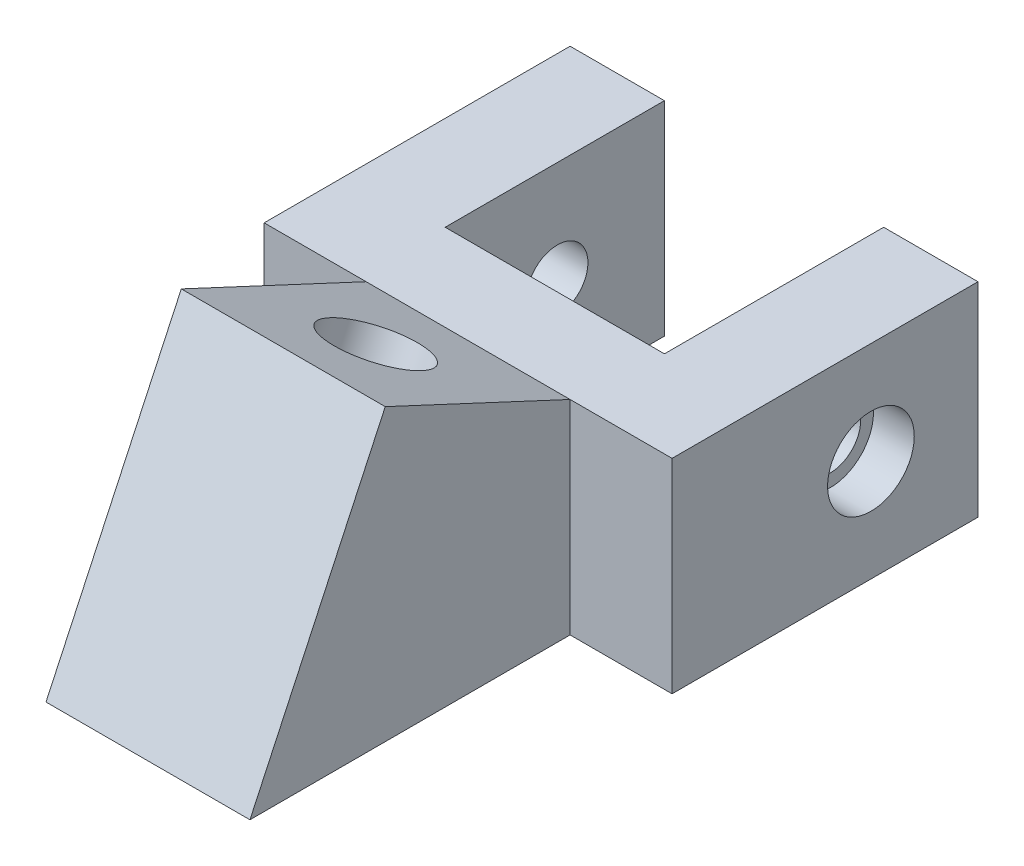
SolidWorks part; units mm, degrees
ref_plane "Front Plane" through (0, 0, 0) normal (0, 0, 1) x (1, 0, 0)
ref_plane "Top Plane" through (0, 0, 0) normal (0, 1, 0) x (1, 0, 0)
ref_plane "Right Plane" through (0, 0, 0) normal (1, 0, 0) x (0, 0, -1)
sketch "Sketch1" plane through (0, 0, 0) normal (0, 1, 0) x (1, 0, 0)
  line L0 (-10.75, 15) -> (-10.75, -6.5)
  line L1 (-20, -15) -> (20, -15)
  line L2 (-20, -15) -> (-20, 15)
  line L3 (-20, 15) -> (-10.75, 15)
  line L4 (20, -15) -> (20, 15)
  line L5 (-20, -15) -> (20, 15) construction
  line L6 (-20, 15) -> (20, -15) construction
  line L7 (-10.75, -6.5) -> (10.75, -6.5)
  line L8 (10.75, -6.5) -> (10.75, 15)
  line L9 (10.75, 15) -> (20, 15)
  point P0 (0, 0)
  dimension "D1" = 40
  dimension "D2" = 30
  dimension "D3" = 21.5
  dimension "D4" = 21.5
  dimension "D5" = 10.75
extrude "Boss-Extrude1" add sketch "Sketch1" along normal blind 20 contours L7 L8 L9 L4 L1 L2 L3 L0
sketch "Sketch2" plane through (0, 0, 0) normal (1, 0, 0) x (0, 0, -1)
  line L0 (-15, 20) -> (-15, 0) construction
  line L1 (-15, 20) -> (-15, 0)
  line L2 (-15, 20) -> (-33.1262, 28.4524)
  line L3 (-33.1262, 28.4524) -> (-46.3937, 0)
  line L5 (-46.3937, 0) -> (-15, 0)
  dimension "D1" = 155
  dimension "D3" = 20
extrude "Boss-Extrude3" add sketch "Sketch2" along normal mid plane 20 contours L2 L3 L5 L1
sketch "Sketch3" plane through (0, 10.6825, -4.9814) normal (0, 0.9063, -0.4226) x (1, 0, 0)
  line L0 (10, -22.047) -> (-10, -22.047) construction
  line L1 (-10, -22.047) -> (-10, -42.047) construction
  circle A0 centre (0, -32.047) radius 4.5
  point P4 (0, -22.047)
  dimension "D1" = 9
  dimension "D2" = 10
  dimension "D3" = 10
extrude "Cut-Extrude1" cut sketch "Sketch3" against normal through all
ref_plane "Plane1" through (0, -10.1625, 4.7389) normal (0, 0.9063, -0.4226) x (1, 0, 0)
sketch "Sketch4" plane through (0, -10.1625, 4.7389) normal (0, 0.9063, -0.4226) x (1, 0, 0)
  line L0 (10, -42.047) -> (-10, -42.047) construction
  line L1 (4.0415, -39.047) -> (8.0829, -32.047)
  line L2 (8.0829, -32.047) -> (4.0415, -25.047)
  line L3 (4.0415, -25.047) -> (-4.0415, -25.047)
  line L4 (-4.0415, -25.047) -> (-8.0829, -32.047)
  line L5 (-8.0829, -32.047) -> (-4.0415, -39.047)
  line L6 (-4.0415, -39.047) -> (4.0415, -39.047)
  circle A0 centre (0, -32.047) radius 7 construction
  dimension "D1" = 14
extrude "Cut-Extrude2" cut sketch "Sketch4" against normal blind 20
sketch "Sketch5" plane through (20, 0, 0) normal (1, 0, 0) x (0, 0, -1)
  line L0 (-15, 0) -> (15, 0) construction
  circle A0 centre (4.5, 10) radius 3
  dimension "D1" = 6
  dimension "D3" = 10
  dimension "D2" = 11
extrude "Cut-Extrude3" cut sketch "Sketch5" against normal through all
sketch "Sketch6" plane through (20, 0, 0) normal (1, 0, 0) x (0, 0, -1)
  circle A0 centre (4.5, 10) radius 4.25
  dimension "D1" = 8.5
extrude "Cut-Extrude4" cut sketch "Sketch6" against normal blind 4
sketch "Sketch7" plane through (-20, 0, 0) normal (-1, 0, 0) x (0, 0, 1)
  circle A0 centre (-4.5, 10) radius 4.25
  dimension "D1" = 8.5
extrude "Cut-Extrude5" cut sketch "Sketch7" against normal blind 4
